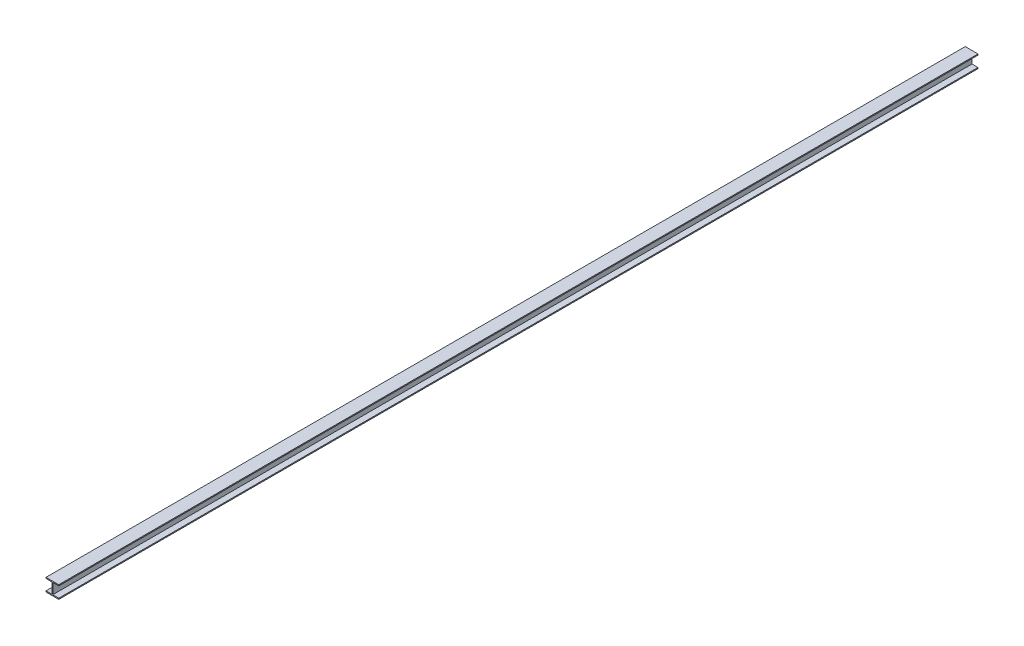
SolidWorks part; units mm, degrees
material "6061 Alloy"
ref_plane "Front Plane" through (0, 0, 0) normal (0, 0, 1) x (1, 0, 0)
ref_plane "Top Plane" through (0, 0, 0) normal (0, 1, 0) x (1, 0, 0)
ref_plane "Right Plane" through (0, 0, 0) normal (1, 0, 0) x (0, 0, -1)
sketch "Sketch1" plane through (0, 0, 0) normal (0, 0, 1) x (1, 0, 0)
  line L0 (-63.5, 116.5352) -> (63.5, 116.5352)
  line L1 (63.5, 116.5352) -> (63.5, 106.0704)
  line L2 (63.5, 106.0704) -> (3.9751, 106.0704)
  line L3 (3.9751, 106.0704) -> (3.9751, 0)
  line L4 (3.9751, 0) -> (63.5, 0)
  line L5 (63.5, 0) -> (63.5, -10.4648)
  line L6 (63.5, -10.4648) -> (-63.5, -10.4648)
  line L7 (-63.5, -10.4648) -> (-63.5, 0)
  line L8 (-63.5, 0) -> (-3.9751, 0)
  line L9 (-3.9751, 0) -> (-3.9751, 106.0704)
  line L10 (-3.9751, 106.0704) -> (-63.5, 106.0704)
  line L11 (-63.5, 106.0704) -> (-63.5, 116.5352)
  line L12 (0, -13.8171) -> (0, 37.3356) construction
  line L13 (-63.5, 12.5984) -> (63.5, 12.5984) construction
  point P13 (0, 116.5352)
  point P16 (0, -10.4648)
  point P19 (0, 12.5984)
  dimension "D1" = 127
  dimension "D2" = 10.4648
  dimension "D3" = 7.9502
  dimension "D4" = 127
  dimension "D5" = 93.472
extrude "RAIL" add sketch "Sketch1" along normal mid plane 9144
sketch "Sketch4" [suppressed] plane through (0, 106.0704, 0) normal (0, -1, 0) x (1, 0, 0)
  line L0 (-25.4, 1828.8) -> (25.4, 1828.8) construction
  line L1 (-57.15, 1831.1876) -> (-25.4, 1831.1876)
  line L2 (-57.15, 1831.1876) -> (-57.15, 1826.4124)
  line L3 (-57.15, 1826.4124) -> (-25.4, 1826.4124)
  line L4 (-25.4, 1831.1876) -> (-25.4, 1826.4124)
  line L5 (25.4, 1831.1876) -> (57.15, 1831.1876)
  line L6 (25.4, 1831.1876) -> (25.4, 1826.4124)
  line L7 (25.4, 1826.4124) -> (57.15, 1826.4124)
  line L8 (57.15, 1831.1876) -> (57.15, 1826.4124)
  line L9 (-25.4, -1828.8) -> (25.4, -1828.8) construction
  line L10 (-57.15, -1826.4124) -> (-25.4, -1826.4124)
  line L11 (-57.15, -1826.4124) -> (-57.15, -1831.1876)
  line L12 (-57.15, -1831.1876) -> (-25.4, -1831.1876)
  line L13 (-25.4, -1826.4124) -> (-25.4, -1831.1876)
  line L14 (25.4, -1826.4124) -> (57.15, -1826.4124)
  line L15 (25.4, -1826.4124) -> (25.4, -1831.1876)
  line L16 (25.4, -1831.1876) -> (57.15, -1831.1876)
  line L17 (57.15, -1826.4124) -> (57.15, -1831.1876)
  line L18 (0, 1828.8) -> (0, -1828.8) construction
  line L20 (63.5, 0) -> (-63.5, 0) construction
  line L21 (63.5, 2743.2) -> (63.5, -2743.2) construction
  line L22 (-63.5, 2743.2) -> (-63.5, -2743.2) construction
  point P22 (0, -1828.8)
  point P23 (0, 1828.8)
  point P36 (0, 0)
  point P37 (0, 0)
  dimension "D1" = 4.7752
  dimension "D2" = 31.75
  dimension "D3" = 50.8
  dimension "D4" = 3657.6
equation "\"c_w_diam\"= 2.5"
equation "\"lever_advantage\"= 2"
equation "\"wheel_separation\"= 12 * 12"
equation "\"D1@CONTACT_wheels\" = \"wheel_separation\""
equation "\"wheel_width\"=4"
equation "\"D2@CONTACT_wheels\" = \"wheel_width\""
equation "\"wheel_contact_length\"=1"
equation "\"D3@CONTACT_wheels\" = \"wheel_contact_length\""
equation "\"clamping_wheel_contact\"= 0.188"
equation "\"D1@Sketch4\"=\"clamping_wheel_contact\""
equation "\"clamping_wheel_width\"= 1.25"
equation "\"D2@Sketch4\"=\"clamping_wheel_width\""
equation "\"clamping_wheel_separation\"= 12 * 12"
equation "\"D4@Sketch4\"=\"clamping_wheel_separation\""
